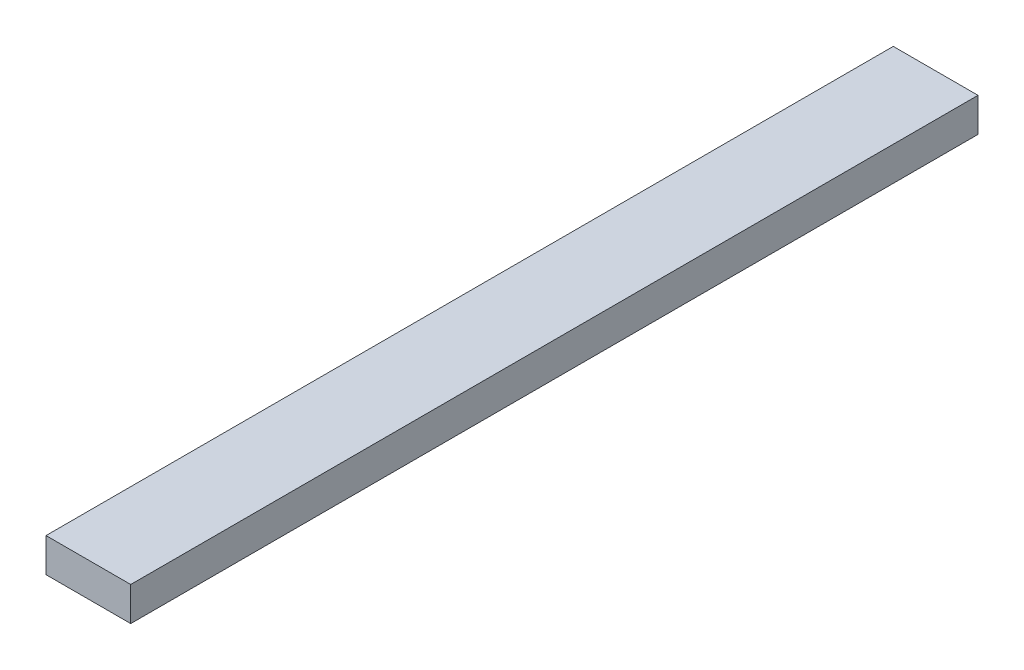
SolidWorks part; units mm, degrees
material "SS400"
ref_plane "正面" through (0, 0, 0) normal (0, 0, 1) x (1, 0, 0)
ref_plane "平面" through (0, 0, 0) normal (0, 1, 0) x (1, 0, 0)
ref_plane "右側面" through (0, 0, 0) normal (1, 0, 0) x (0, 0, -1)
sketch "ｽｹｯﾁ1" plane through (0, 0, 0) normal (0, 0, 1) x (1, 0, 0)
  line L1 (-25, 10) -> (25, 10)
  line L2 (-25, 10) -> (-25, -10)
  line L3 (-25, -10) -> (25, -10)
  line L4 (25, 10) -> (25, -10)
  line L5 (-25, 10) -> (25, -10) construction
  line L6 (-25, -10) -> (25, 10) construction
  point P0 (0, 0)
  dimension "D1" = 50
  dimension "D2" = 20
extrude "ﾎﾞｽ - 押し出し1" add sketch "ｽｹｯﾁ1" along normal blind 500
